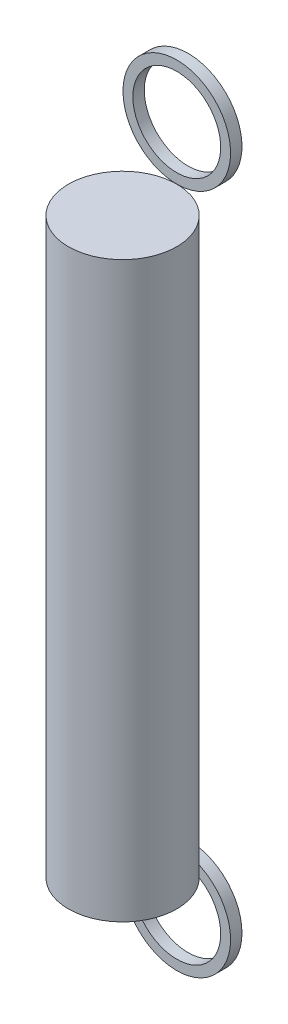
SolidWorks part; units mm, degrees
ref_plane "Front Plane" through (0, 0, 0) normal (0, 0, 1) x (1, 0, 0)
ref_plane "Top Plane" through (0, 0, 0) normal (0, 1, 0) x (1, 0, 0)
ref_plane "Right Plane" through (0, 0, 0) normal (1, 0, 0) x (0, 0, -1)
sketch "Sketch1" plane through (0, 0, 0) normal (0, 1, 0) x (1, 0, 0)
  circle A0 centre (0, 0) radius 3.425
  dimension "D1" = 6.85
extrude "Boss-Extrude1" add sketch "Sketch1" along normal blind 36.25
ref_plane "Plane1" through (0, 0, -3.425) normal (0, 0, -1) x (-1, 0, 0)
sketch "Sketch2" plane through (0, 0, -3.425) normal (0, 0, -1) x (-1, 0, 0)
  line L0 (-13.6409, 18.125) -> (20.4909, 18.125) construction
  line L3 (3.425, 0) -> (3.425, 36.25) construction
  line L5 (3.425, 36.25) -> (-3.425, 36.25) construction
  circle A0 centre (0, 39.65) radius 3.4
  circle A1 centre (0, 39.65) radius 2.775
  circle A2 centre (0, -3.4) radius 2.775
  circle A3 centre (0, -3.4) radius 3.4
  point P7 (0, 0)
  point P9 (3.425, 18.125)
  point P11 (0, 0)
  dimension "D1" = 6.8
  dimension "D2" = 5.55
extrude "Boss-Extrude2" add sketch "Sketch2" along normal blind 0.72 separate body
